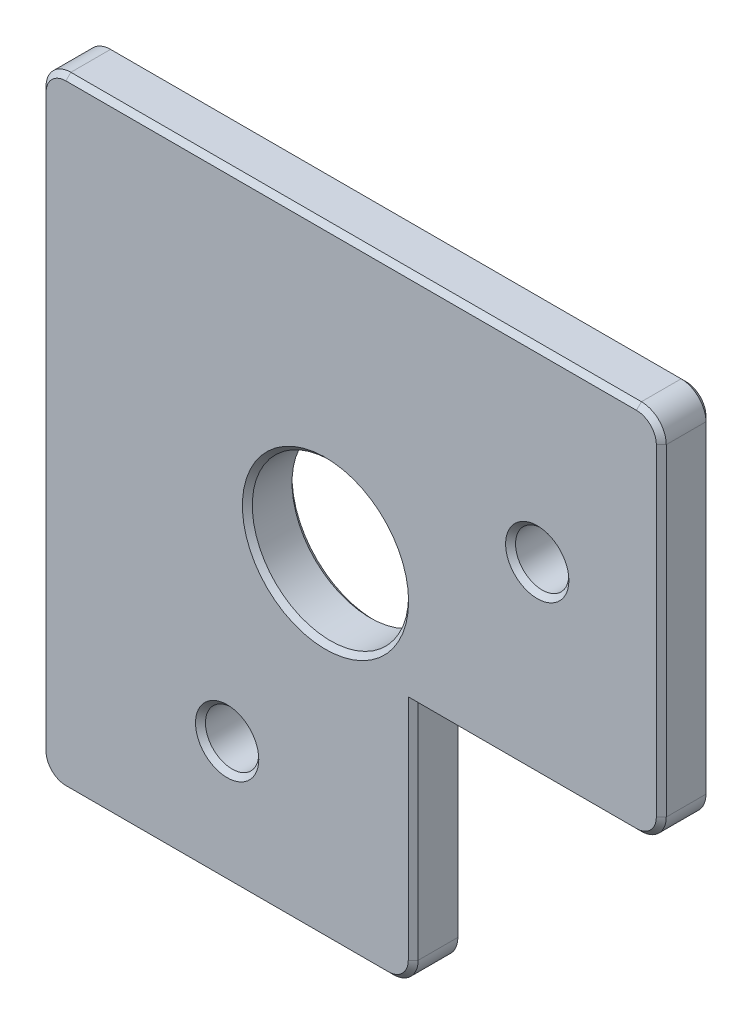
SolidWorks part; units mm, degrees
ref_plane "Front Plane" through (0, 0, 0) normal (0, 0, 1) x (1, 0, 0)
ref_plane "Top Plane" through (0, 0, 0) normal (0, 1, 0) x (1, 0, 0)
ref_plane "Right Plane" through (0, 0, 0) normal (1, 0, 0) x (0, 0, -1)
sketch "Sketch1" plane through (0, 0, 0) normal (0, 0, 1) x (1, 0, 0)
  line L1 (0, -50) -> (30, -50)
  line L2 (30, -50) -> (30, -30)
  line L3 (30, -30) -> (50, -30)
  line L4 (50, -30) -> (50, 0)
  line L5 (50, 0) -> (0, 0)
  line L7 (0, -50) -> (0, 0)
  line L8 (0, 0) -> (30, -30) construction
  line L9 (40, -30) -> (40, 0) construction
  line L10 (30, -40) -> (0, -40) construction
  line L11 (30, -30) -> (30, 0) construction
  circle A0 centre (15, -40) radius 2.15
  circle A1 centre (40, -15) radius 2.15
  circle A2 centre (22.9289, -22.9289) radius 6.3
  point P18 (22.9183, -22.9183)
  dimension "D5" = 4.3
  dimension "D6" = 12.6
  dimension "D1" = 20
  dimension "D2" = 20
  dimension "D3" = 45
  dimension "D4" = 30
  dimension "D7" = 10
extrude "Boss-Extrude1" add sketch "Sketch1" along normal blind 4
fillet "Fillet1" radius 2 5 edges at (0, 0, 2) (50, 0, 2) (50, -30, 2) (0, -50, 2) (30, -50, 2)
chamfer "Chamfer1" distance 0.4 angle 45 28 edges at (42.15, -15, 4) (49.4142, -0.5858, 4) (50, -15, 4) (49.4142, -29.4142, 4) (39, -30, 4) (30, -39, 4) (29.4142, -49.4142, 4) (15, -50, 4) (0.5858, -49.4142, 4) (0, -25, 4) (0.5858, -0.5858, 4) (25, 0, 4) (17.15, -40, 4) (42.15, -15, 0) (17.15, -40, 0) (0.5858, -49.4142, 0) (15, -50, 0) (29.4142, -49.4142, 0) (30, -39, 0) (39, -30, 0) (49.4142, -29.4142, 0) (50, -15, 0) (49.4142, -0.5858, 0) (25, 0, 0) (0.5858, -0.5858, 0) (0, -25, 0) (29.2289, -22.9289, 4) (29.2289, -22.9289, 0)
